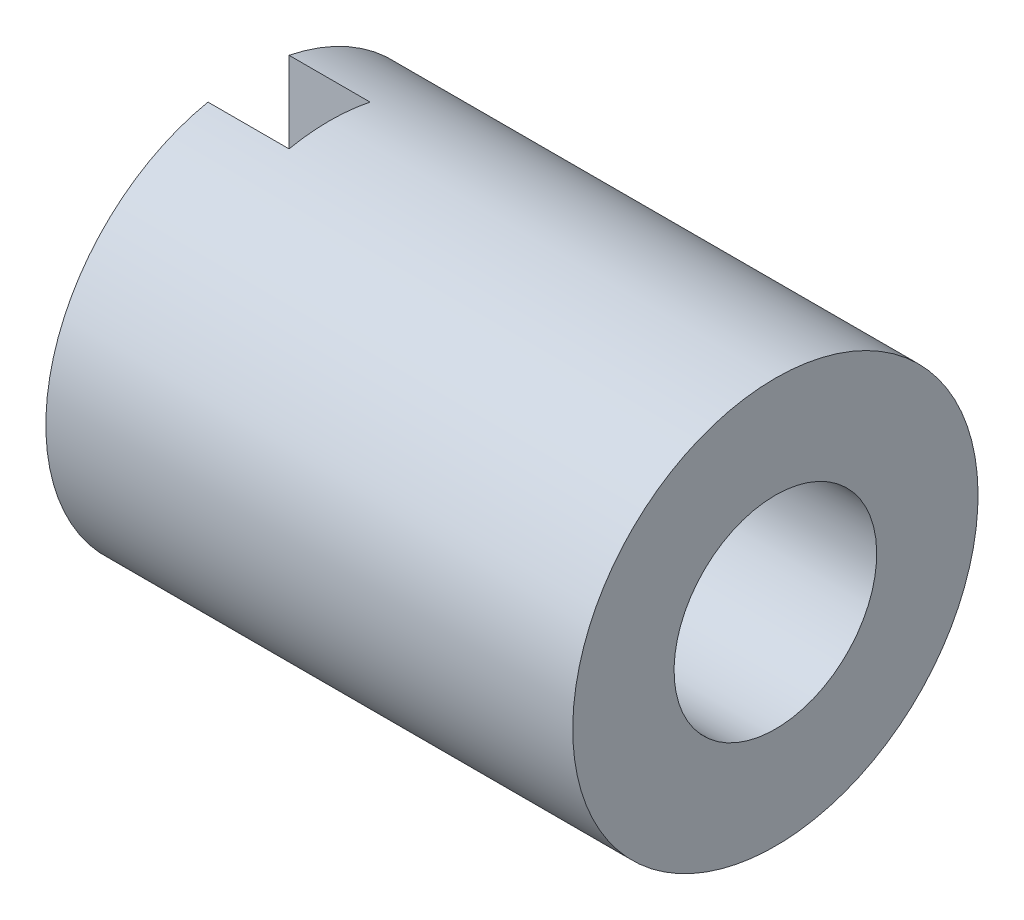
SolidWorks part; units mm, degrees
material "7075-T6 (SN)"
ref_plane "Front Plane" through (0, 0, 0) normal (0, 0, 1) x (1, 0, 0)
ref_plane "Top Plane" through (0, 0, 0) normal (0, 1, 0) x (1, 0, 0)
ref_plane "Right Plane" through (0, 0, 0) normal (1, 0, 0) x (0, 0, -1)
sketch "Sketch1" plane through (0, 0, 0) normal (0, 0, 1) x (1, 0, 0)
  line L0 (0, 0) -> (0, 2.5)
  line L1 (0, 2.5) -> (6.5, 2.5)
  line L2 (6.5, 2.5) -> (6.5, 1.25)
  line L3 (6.5, 1.25) -> (2, 1.25)
  line L4 (2, 1.25) -> (2, 0)
  line L5 (2, 0) -> (0, 0)
  dimension "D1" = 2.5
  dimension "D2" = 1.25
  dimension "D3" = 6.5
  dimension "D4" = 4.5
revolve "Revolve1" add sketch "Sketch1" angle 360 about L5
sketch "Sketch2" plane through (0, 0, 0) normal (-1, 0, 0) x (0, 0, 1)
  line L1 (-0.5, -2.5) -> (0.5, -2.5)
  line L2 (-0.5, -2.5) -> (-0.5, 2.5)
  line L3 (-0.5, 2.5) -> (0.5, 2.5)
  line L4 (0.5, -2.5) -> (0.5, 2.5)
  line L5 (-0.5, -2.5) -> (0.5, 2.5) construction
  line L6 (-0.5, 2.5) -> (0.5, -2.5) construction
  circle A0 centre (0, 0) radius 2.5 construction
  point P0 (0, 0)
  dimension "D1" = 1
extrude "Cut-Extrude1" cut sketch "Sketch2" against normal blind 1
